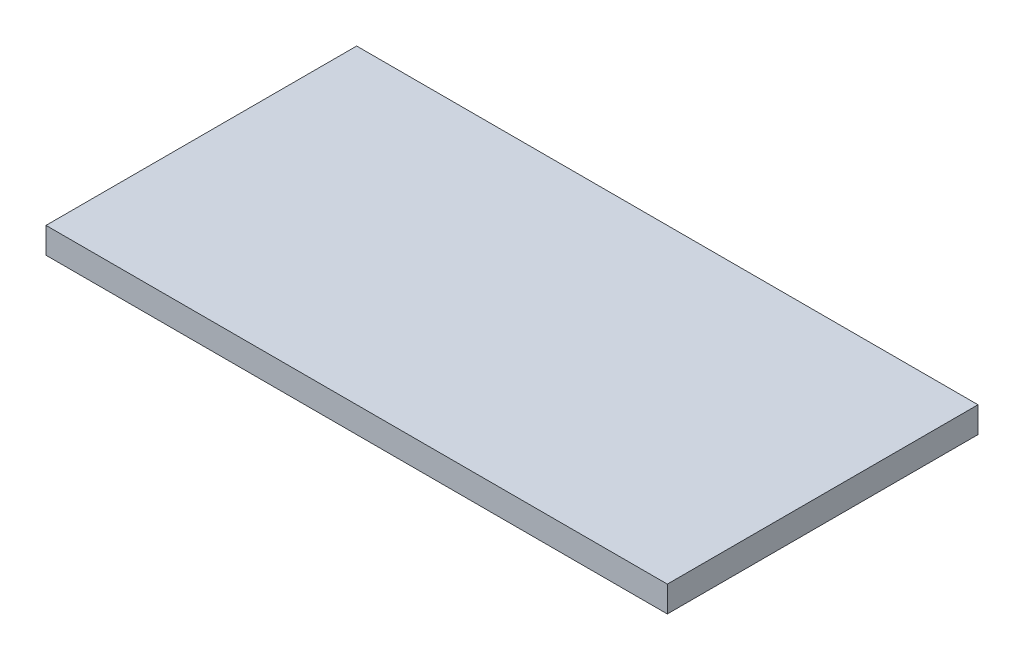
SolidWorks part; units mm, degrees
ref_plane "Спереди" through (0, 0, 0) normal (0, 0, 1) x (1, 0, 0)
ref_plane "Сверху" through (0, 0, 0) normal (0, 1, 0) x (1, 0, 0)
ref_plane "Справа" through (0, 0, 0) normal (1, 0, 0) x (0, 0, -1)
sketch "Эскиз1" plane through (0, 0, 0) normal (0, 1, 0) x (1, 0, 0)
  line L1 (0, 0) -> (1200, 0)
  line L2 (0, 0) -> (0, 600)
  line L3 (0, 600) -> (1200, 600)
  line L4 (1200, 0) -> (1200, 600)
extrude "Бобышка-Вытянуть1" add sketch "Эскиз1" along normal blind 50
